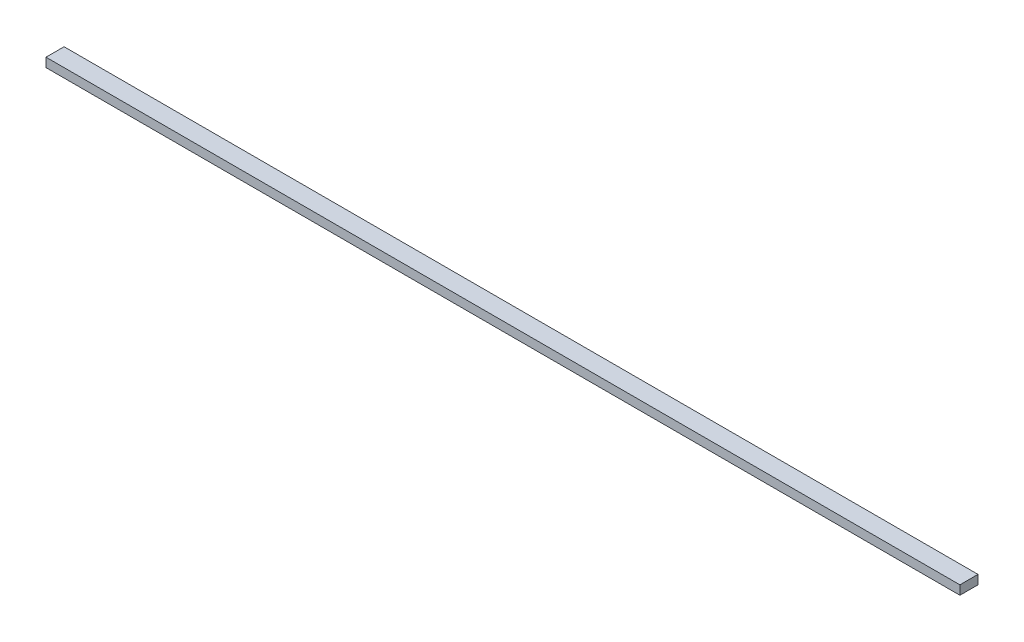
SolidWorks part; units mm, degrees
ref_plane "Front Plane" through (0, 0, 0) normal (0, 0, 1) x (1, 0, 0)
ref_plane "Top Plane" through (0, 0, 0) normal (0, 1, 0) x (1, 0, 0)
ref_plane "Right Plane" through (0, 0, 0) normal (1, 0, 0) x (0, 0, -1)
sketch "Sketch1" plane through (0, 0, 0) normal (0, 1, 0) x (1, 0, 0)
  line L0 (-505, 10) -> (505, -10) construction
  line L1 (-505, 10) -> (505, 10)
  line L2 (-505, 10) -> (-505, -10)
  line L3 (-505, -10) -> (505, -10)
  line L4 (505, 10) -> (505, -10)
  dimension "D1" = 1010
  dimension "D2" = 20
extrude "Boss-Extrude1" add sketch "Sketch1" along normal blind 10
